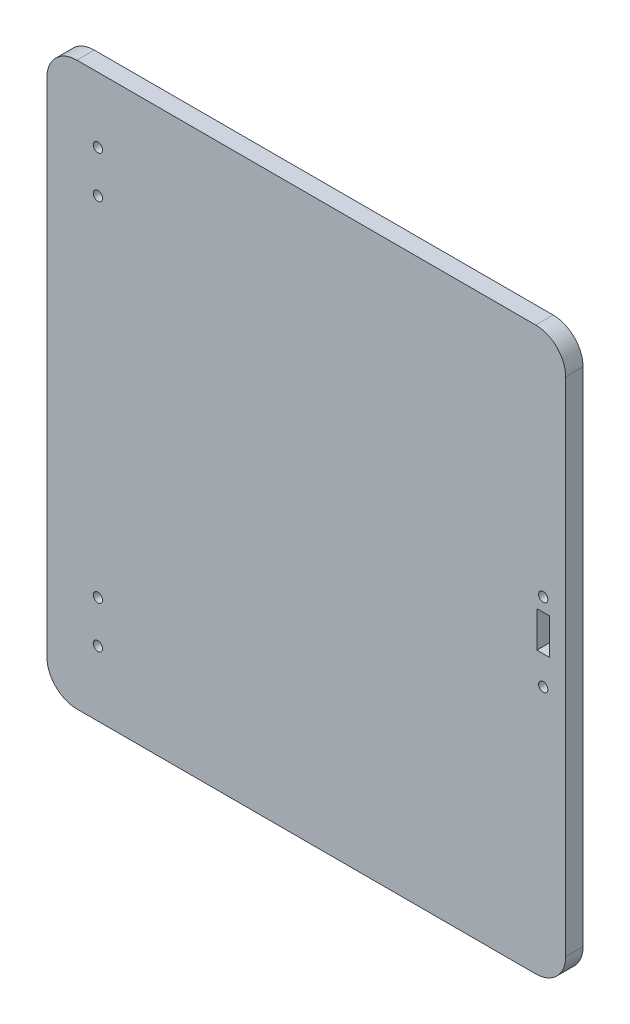
SolidWorks part; units mm, degrees
material "Acrylic (Medium-high impact)"
ref_plane "Front" through (0, 0, 0) normal (0, 0, 1) x (1, 0, 0)
ref_plane "Top" through (0, 0, 0) normal (0, 1, 0) x (1, 0, 0)
ref_plane "Right" through (0, 0, 0) normal (1, 0, 0) x (0, 0, -1)
sketch "Sketch2" plane through (0, 0, 0) normal (0, 0, 1) x (1, 0, 0)
  line L4 (76.5, 93.7) -> (-76.5, 93.7)
  line L5 (-86.5, 83.7) -> (-86.5, -83.7)
  line L6 (76.5, -93.7) -> (-76.5, -93.7)
  line L7 (86.5, 83.7) -> (86.5, -83.7)
  arc A4 (-76.5, 93.7) -> (-86.5, 83.7) centre (-76.5, 83.7) ccw
  arc A5 (-86.5, -83.7) -> (-76.5, -93.7) centre (-76.5, -83.7) ccw
  arc A6 (76.5, -93.7) -> (86.5, -83.7) centre (76.5, -83.7) ccw
  arc A7 (86.5, 83.7) -> (76.5, 93.7) centre (76.5, 83.7) ccw
  point P3 (0, 0)
  point P5 (0, 0)
  point P8 (86.5, 0)
  point P11 (0, -93.7)
  dimension "D3" = 10
  dimension "D1" = 173
  dimension "D2" = 187.4
extrude "Boss-Extrude1" add sketch "Sketch2" along normal blind 5.8
sketch "Sketch3" plane through (0, 0, 5.8) normal (0, 0, 1) x (1, 0, 0)
  line L0 (-86.5, 83.7) -> (-86.5, -83.7) construction
  line L1 (81.1, 0) -> (76.9, 0)
  line L2 (81.1, 0) -> (81.1, 12)
  line L3 (81.1, 12) -> (76.9, 12)
  line L4 (76.9, 0) -> (76.9, 12)
  point P7 (79, 12)
  dimension "D1" = 4.2
  dimension "D2" = 12
  dimension "D3" = 165.5
extrude "Cut-Extrude1" cut sketch "Sketch3" against normal blind 6.35
sketch "Sketch4" plane through (0, 0, 5.8) normal (0, 0, 1) x (1, 0, 0)
  line L0 (-86.5, 0) -> (86.5, 0) construction
  line L1 (-86.5, 83.7) -> (-86.5, -83.7) construction
  line L2 (86.5, -83.7) -> (86.5, 83.7) construction
  line L3 (-69.5, 72) -> (-69.5, 58) construction
  line L4 (-69.5, -72) -> (-69.5, -58) construction
  circle A0 centre (-69.5, 72) radius 1.55
  circle A1 centre (-69.5, 58) radius 1.55
  circle A2 centre (-69.5, -58) radius 1.55
  circle A3 centre (-69.5, -72) radius 1.55
  point P14 (-69.5, 65)
  dimension "D1" = 3.1
  dimension "D2" = 17
  dimension "D3" = 65
  dimension "D4" = 14
extrude "Cut-Extrude2" cut sketch "Sketch4" against normal through all
sketch "Sketch5" plane through (0, 0, 5.8) normal (0, 0, 1) x (1, 0, 0)
  line L0 (81.1, 12) -> (76.9, 12) construction
  line L1 (76.9, 0) -> (81.1, 0) construction
  circle A0 centre (79, 16.45) radius 1.55
  circle A1 centre (79, -9.55) radius 1.55
  point P9 (79, 12)
  dimension "D1" = 3.1
  dimension "D2" = 4.45
  dimension "D3" = 9.55
extrude "Cut-Extrude3" cut sketch "Sketch5" against normal through all
